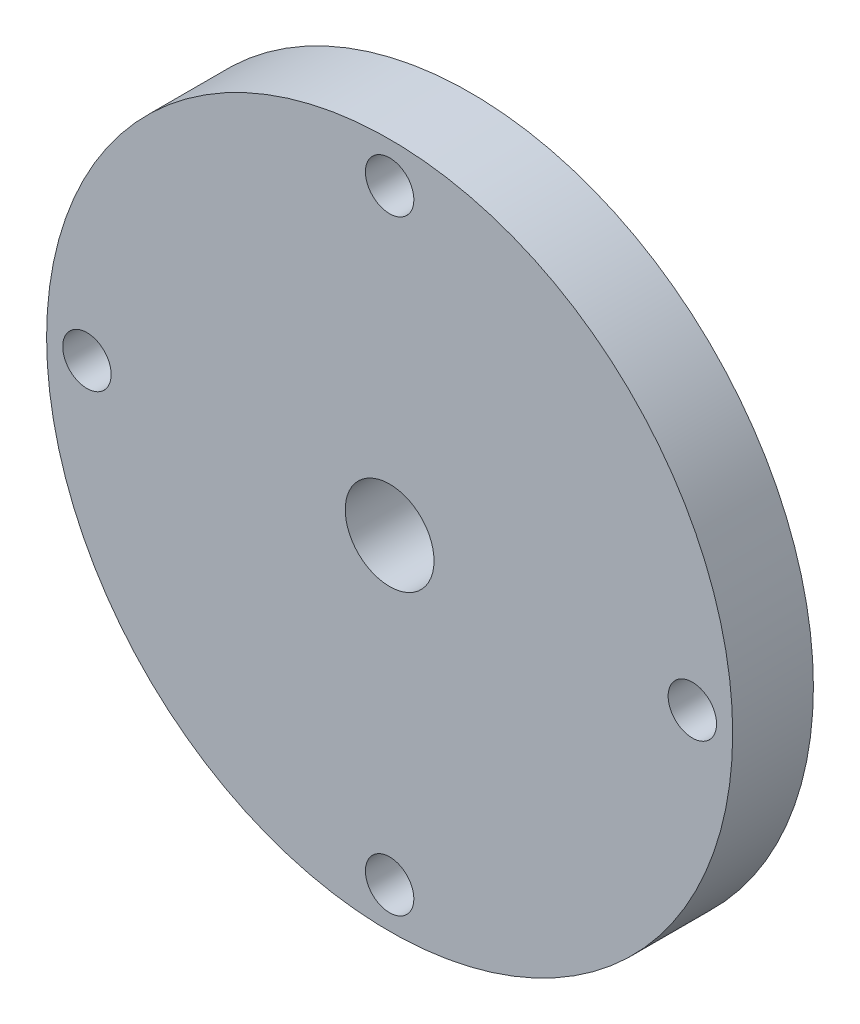
SolidWorks part; units mm, degrees
ref_plane "Plan de face" through (0, 0, 0) normal (0, 0, 1) x (1, 0, 0)
ref_plane "Plan de dessus" through (0, 0, 0) normal (0, 1, 0) x (1, 0, 0)
ref_plane "Plan de droite" through (0, 0, 0) normal (1, 0, 0) x (0, 0, -1)
sketch "Esquisse1" plane through (0, 0, 0) normal (0, 0, 1) x (1, 0, 0)
  circle A0 centre (0, 0) radius 4.25
  circle A1 centre (0, 3.75) radius 0.3
  circle A2 centre (0, 0) radius 0.55
  circle A3 centre (3.75, 0) radius 0.3
  circle A4 centre (0, -3.75) radius 0.3
  circle A5 centre (-3.75, 0) radius 0.3
  point P15 (0, 0)
  dimension "D1" = 8.5
  dimension "D2" = 0.6
  dimension "D3" = 1.1
  dimension "D4" = 4
extrude "Boss.-Extru.1" add sketch "Esquisse1" along normal blind 1
